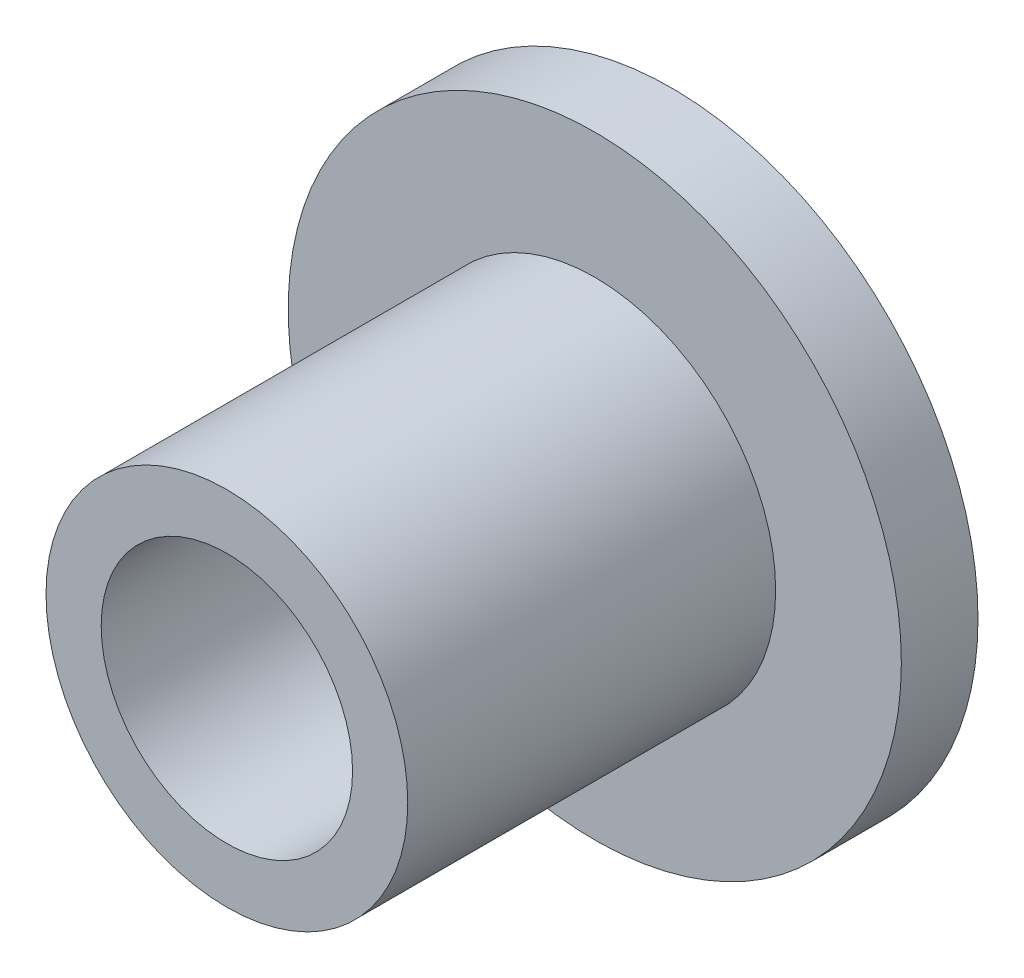
SolidWorks part; units mm, degrees
ref_plane "Front Plane" through (0, 0, 0) normal (0, 0, 1) x (1, 0, 0)
ref_plane "Top Plane" through (0, 0, 0) normal (0, 1, 0) x (1, 0, 0)
ref_plane "Right Plane" through (0, 0, 0) normal (1, 0, 0) x (0, 0, -1)
sketch "Sketch1" plane through (0, 0, 0) normal (0, 0, 1) x (1, 0, 0)
  circle A0 centre (0, 0) radius 5
  dimension "D1" = 10
extrude "Boss-Extrude1" add sketch "Sketch1" along normal blind 1.25
sketch "Sketch2" plane through (0, 0, 1.25) normal (0, 0, 1) x (1, 0, 0)
  circle A0 centre (0, 0) radius 2.95
  circle A1 centre (0, 0) radius 2.05
  dimension "D1" = 5.9
  dimension "D2" = 4.1
extrude "Boss-Extrude2" add sketch "Sketch2" along normal blind 6
sketch "Sketch4" plane through (0, 0, 1.25) normal (0, 0, 1) x (1, 0, 0)
  circle A0 centre (0, 0) radius 2.05
  dimension "D1" = 4.1
extrude "Cut-Extrude3" cut sketch "Sketch4" against normal through all
sketch "Sketch5" plane through (0, 0, 0) normal (0, 0, -1) x (-1, 0, 0)
  circle A0 centre (0, 0) radius 3.05
  dimension "D1" = 6.1
extrude "Cut-Extrude4" cut sketch "Sketch5" against normal blind 0.6
